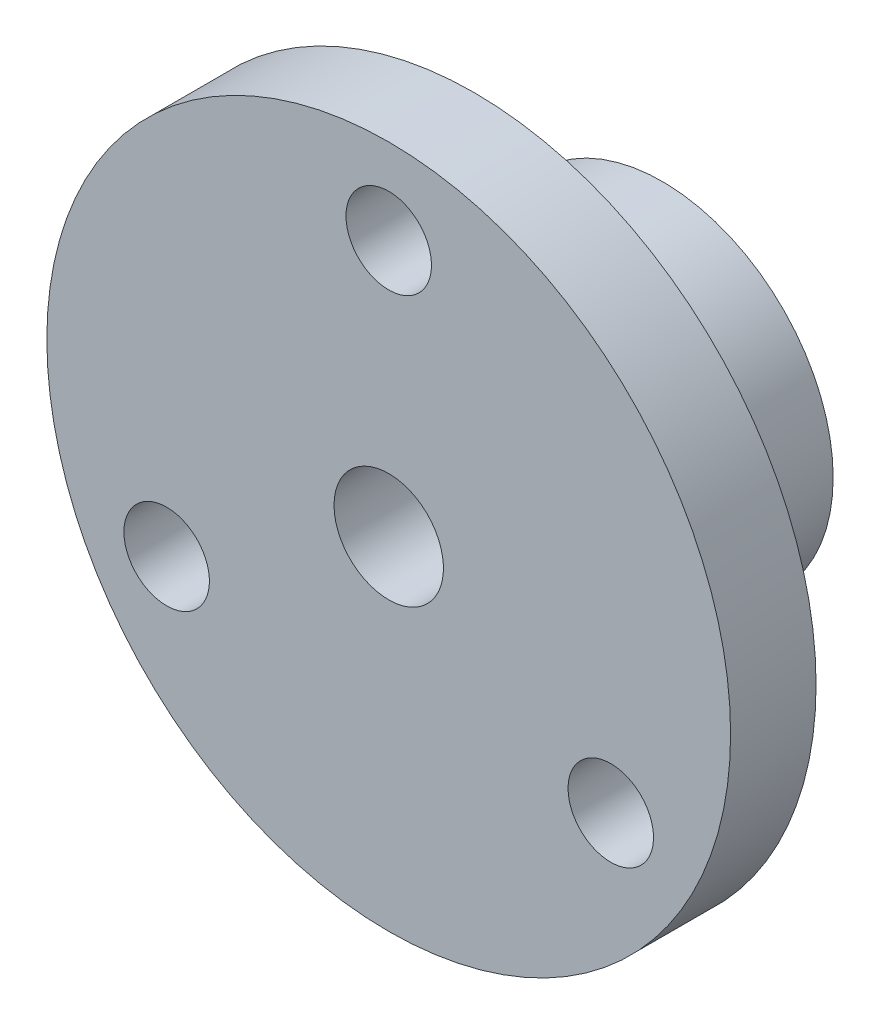
SolidWorks part; units mm, degrees
ref_plane "Front Plane" through (0, 0, 0) normal (0, 0, 1) x (1, 0, 0)
ref_plane "Top Plane" through (0, 0, 0) normal (0, 1, 0) x (1, 0, 0)
ref_plane "Right Plane" through (0, 0, 0) normal (1, 0, 0) x (0, 0, -1)
sketch "Sketch1" plane through (0, 0, 0) normal (1, 0, 0) x (0, 0, -1)
  line L0 (0, 12.7) -> (-13.97, 12.7)
  line L1 (0, 55) -> (0, -55) construction
  line L2 (-13.97, 12.7) -> (-13.97, 25.4)
  line L3 (-13.97, 25.4) -> (-20.32, 25.4)
  line L4 (-20.32, 25.4) -> (-20.32, 0)
  line L5 (-20.32, 0) -> (0, 0)
  line L6 (0, 0) -> (0, 12.7)
  line L7 (55, 0) -> (-55, 0) construction
  dimension "D1" = 6.35
  dimension "D2" = 13.97
  dimension "D3" = 12.7
  dimension "D4" = 12.7
revolve "Revolve1" add sketch "Sketch1" angle 360 about L5
sketch "Sketch3" plane through (0, 0, 0) normal (0, 0, -1) x (-1, 0, 0)
  circle A0 centre (0, 0) radius 4.064
  circle A1 centre (0, 0) radius 12.7 construction
  dimension "D1" = 8.128
extrude "Cut-Extrude1" cut sketch "Sketch3" against normal through all
hole_wizard "1/4-20 Tapped Hole1" positions "3DSketch1" profile "Sketch6" tap size "1/4-20" standard "ANSI Inch"
sketch3d "3DSketch1"
  point P0 (0, 12.7, 7.62)
  dimension "D1" = 12.7
cosmetic thread "Hole Thread1" parameters "D1"=9.5378, "D2"=6.35
sketch "Sketch6" plane through (0, 12.7, 7.62) normal (1, 0, 0) x (0, 0, 1)
  line L0 (0, 0) -> (0, 11.6938)
  line L1 (0, 11.6938) -> (2.5527, 10.16)
  line L2 (2.5527, 10.16) -> (2.5527, 0)
  line L5 (2.5527, 0) -> (0, 0)
  line L10 (0, 11.6938) -> (-2.5527, 10.16) construction
  line L11 (0, -6.35) -> (0, 107.95) construction
  dimension "Tap Drill Dia." = 5.1054
  dimension "Tap Drill Depth" = 10.16
  dimension "Drill Angle" = 118
hole_wizard "1/4 (0.25) Diameter Hole1" positions "3DSketch2" profile "Sketch7" hole size "1/4" standard "ANSI Inch"
sketch3d "3DSketch2"
  circle A0 centre (0, 0, 13.97) radius 25.4 construction
  point P0 (0, 19.05, 13.97)
  point P5 (0, 0, 39.37)
  dimension "D1" = 19.05
sketch "Sketch7" plane through (0, 19.05, 13.97) normal (1, 0, 0) x (0, 1, 0)
  line L0 (0, 0) -> (0, 20.9577)
  line L1 (0, 20.9577) -> (3.175, 19.05)
  line L2 (3.175, 19.05) -> (3.175, 0)
  line L5 (3.175, 0) -> (0, 0)
  line L10 (0, 20.9577) -> (-3.175, 19.05) construction
  line L11 (0, -6.35) -> (0, 107.95) construction
  dimension "Hole Dia." = 6.35
  dimension "Hole Depth" = 19.05
  dimension "Drill Angle" = 118
pattern_circular "CirPattern1" count 3 over 360 about axis through (0, 0, 0) along (0, 0, 1) of "1/4 (0.25) Diameter Hole1"
